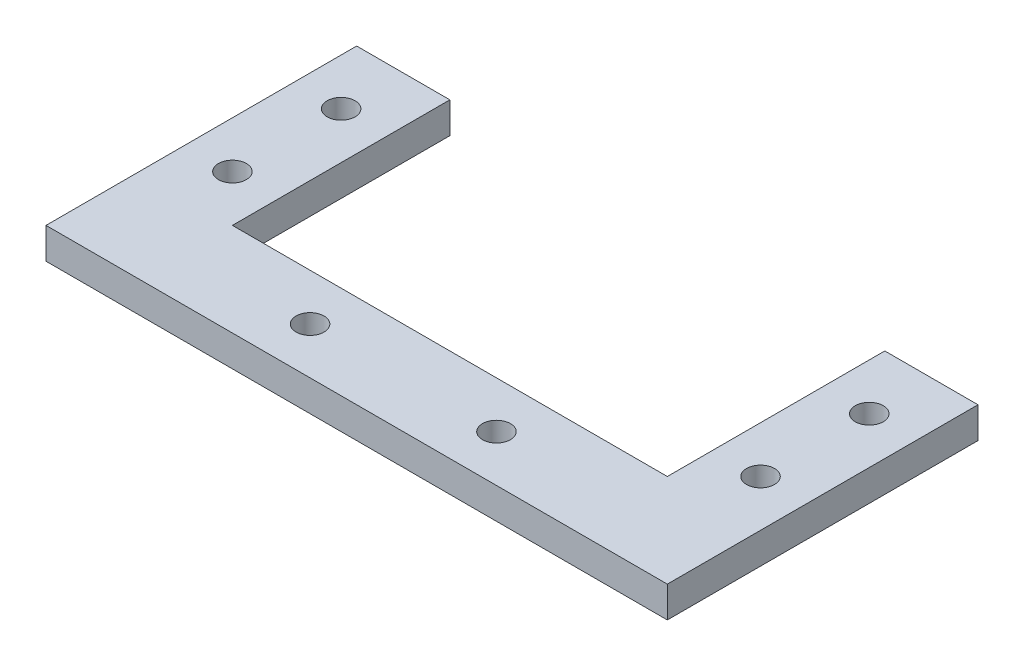
SolidWorks part; units mm, degrees
ref_plane "Front Plane" through (0, 0, 0) normal (0, 0, 1) x (1, 0, 0)
ref_plane "Top Plane" through (0, 0, 0) normal (0, 1, 0) x (1, 0, 0)
ref_plane "Right Plane" through (0, 0, 0) normal (1, 0, 0) x (0, 0, -1)
sketch "Sketch1" plane through (0, 0, 0) normal (0, 1, 0) x (1, 0, 0)
  line L36 (0, 0) -> (-200, 0)
  line L37 (-200, 0) -> (-200, 100)
  line L38 (-200, 100) -> (-170, 100)
  line L39 (-170, 100) -> (-170, 30)
  line L40 (-170, 30) -> (-30, 30)
  line L41 (-30, 30) -> (-30, 100)
  line L42 (-30, 100) -> (0, 100)
  line L43 (0, 100) -> (0, 0)
  circle A0 centre (-15, 80) radius 4.5
  circle A1 centre (-15, 45) radius 4.5
  circle A2 centre (-130, 15) radius 4.5
  circle A3 centre (-70, 15) radius 4.5
  circle A4 centre (-185, 80) radius 4.5
  circle A5 centre (-185, 45) radius 4.5
extrude "Boss-Extrude1" add sketch "Sketch1" along normal blind 10
